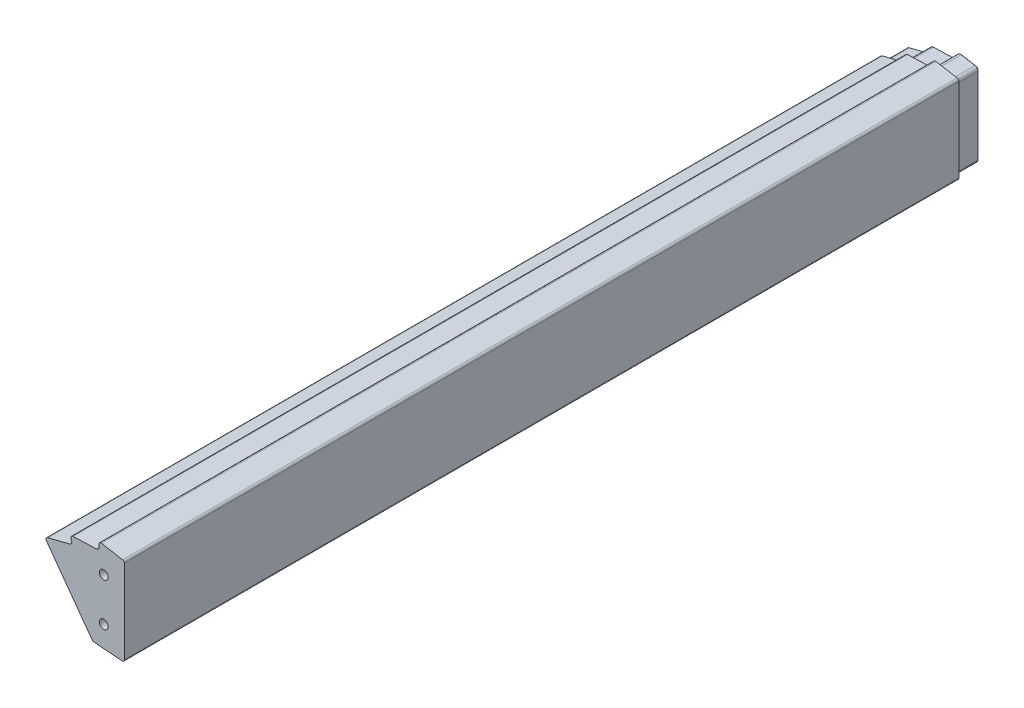
SolidWorks part; units mm, degrees
material "ladder carbon corrected"
ref_plane "Front Plane" through (0, 0, 0) normal (0, 0, 1) x (1, 0, 0)
ref_plane "Top Plane" through (0, 0, 0) normal (0, 1, 0) x (1, 0, 0)
ref_plane "Right Plane" through (0, 0, 0) normal (1, 0, 0) x (0, 0, -1)
sketch "Sketch1" plane through (0, 0, 0) normal (0, 0, 1) x (1, 0, 0)
  line L0 (-19.1269, 28.9196) -> (-2.6193, 27.602)
  line L1 (-46.8997, 66.2532) -> (-20.221, 29.5332)
  line L2 (-46.0481, 68.5905) -> (-33.2024, 71.7845)
  line L3 (-31.1768, 76.652) -> (-17.552, 77.119)
  line L4 (-1, 77.8014) -> (-1, 29.0973)
  line L5 (-14.5587, 81.459) -> (-2.2386, 79.2785)
  line L6 (0, 0) -> (-21.3966, 104.6618) construction
  line L7 (0, 0) -> (-41.6883, 95.6295) construction
  line L8 (-19.7813, 28.3232) -> (5.0398, 26.3421) construction
  line L9 (0, 0) -> (2.1211, 26.575) construction
  line L10 (-30.1863, 29.8023) -> (12.2556, 26.4148) construction
  line L11 (-19.7813, 28.3232) -> (-19.7378, 28.868) construction
  line L12 (-46.4094, 27.8735) -> (21.976, 24.7628) construction
  line L13 (0, 0) -> (0, 116.6603) construction
  line L15 (0, 0) -> (-56.299, 77.489) construction
  line L19 (-16.2897, 79.6815) -> (-16.1338, 78.9186)
  line L20 (-32.5005, 74.5535) -> (-32.1893, 73.8396)
  arc A0 (-33.2024, 71.7845) -> (-32.1893, 73.8396) centre (-33.5643, 73.2402) ccw
  arc A1 (-31.1768, 76.652) -> (-32.5005, 74.5535) centre (-31.1255, 75.1529) ccw
  arc A2 (-17.552, 77.119) -> (-16.1338, 78.9186) centre (-17.6034, 78.6181) ccw
  arc A3 (-14.5587, 81.459) -> (-16.2897, 79.6815) centre (-14.8201, 79.982) ccw
  arc A4 (-2.2386, 79.2785) -> (-1, 77.8014) centre (-2.5, 77.8014) cw
  arc A5 (-46.0481, 68.5905) -> (-46.8997, 66.2532) centre (-45.6861, 67.1348) ccw
  arc A6 (-19.1269, 28.9196) -> (-20.221, 29.5332) centre (-19.0075, 30.4148) cw
  arc A7 (-1, 29.0973) -> (-2.6193, 27.602) centre (-2.5, 29.0973) cw
  circle A8 centre (0, 0) radius 77.675 construction
  dimension "D1" = 1.5
  dimension "D2" = 1.5
  dimension "D11" = 155.35
  dimension "D3" = 2.928
  dimension "D4" = 26.6595
  dimension "D5" = 27.3061
  dimension "D6" = 24.9
  dimension "D7" = 0.5466
  dimension "D8" = 36
  dimension "D9" = 85.437
  dimension "D10" = 1
  dimension "D12" = 11.554
  dimension "D13" = 12
  dimension "D14" = 79.963
  dimension "D15" = 12
  dimension "D16" = 12
extrude "Extrude-Thin1" add sketch "Sketch1" along normal blind 137.5002 and the other way blind 213.5 thin thin type one direction reverse wall 0.27
sketch "Sketch2" plane through (0, 0, 0) normal (0, 0, 1) x (1, 0, 0)
  line L0 (-46.6812, 66.4119) -> (-20.0026, 29.6919) construction
  line L1 (-19.1054, 29.1887) -> (-2.5979, 27.8712) construction
  line L2 (-1.27, 29.0973) -> (-1.27, 77.8014) construction
  line L3 (-46.6812, 66.4119) -> (-20.0026, 29.6919)
  line L4 (-19.1054, 29.1887) -> (-2.5979, 27.8712)
  line L5 (-1.27, 29.0973) -> (-1.27, 77.8014)
  line L6 (-46.6812, 66.4119) -> (-46.7308, 66.48)
  line L31 (-1.27, 77.9505) -> (-1.27, 77.8014)
  line L36 (-2.2638, 79.1357) -> (-14.584, 81.3162)
  line L37 (-16.1477, 79.7106) -> (-15.9917, 78.9476)
  line L38 (-17.547, 76.9741) -> (-31.1719, 76.5071)
  line L39 (-32.3676, 74.6114) -> (-32.0564, 73.8976)
  line L40 (-33.1674, 71.6438) -> (-46.0131, 68.4498)
  line L41 (-2.2638, 79.1357) -> (-14.584, 81.3162)
  line L42 (-16.1477, 79.7106) -> (-15.9917, 78.9476)
  line L43 (-17.547, 76.9741) -> (-31.1719, 76.5071)
  line L44 (-32.3676, 74.6114) -> (-32.0564, 73.8976)
  line L45 (-33.1674, 71.6438) -> (-46.0131, 68.4498)
  arc A0 (-20.0026, 29.6919) -> (-19.1054, 29.1887) centre (-19.0075, 30.4148) ccw construction
  arc A1 (-2.5979, 27.8712) -> (-1.27, 29.0973) centre (-2.5, 29.0973) ccw construction
  arc A2 (-20.0026, 29.6919) -> (-19.1054, 29.1887) centre (-19.0075, 30.4148) ccw
  arc A3 (-2.5979, 27.8712) -> (-1.27, 29.0973) centre (-2.5, 29.0973) ccw
  arc A24 (-46.0131, 68.4498) -> (-46.7308, 66.48) centre (-45.7081, 67.2231) ccw
  arc A25 (-2.2638, 79.1357) -> (-1.27, 77.9505) centre (-2.4736, 77.9505) cw
  arc A28 (-14.584, 81.3162) -> (-16.1477, 79.7106) centre (-14.8201, 79.982) ccw
  arc A29 (-17.547, 76.9741) -> (-15.9917, 78.9476) centre (-17.6034, 78.6181) ccw
  arc A30 (-31.1719, 76.5071) -> (-32.3676, 74.6114) centre (-31.1255, 75.1529) ccw
  arc A31 (-33.1674, 71.6438) -> (-32.0564, 73.8976) centre (-33.5643, 73.2402) ccw
  arc A32 (-14.584, 81.3162) -> (-16.1477, 79.7106) centre (-14.8201, 79.982) ccw
  arc A33 (-17.547, 76.9741) -> (-15.9917, 78.9476) centre (-17.6034, 78.6181) ccw
  arc A34 (-31.1719, 76.5071) -> (-32.3676, 74.6114) centre (-31.1255, 75.1529) ccw
  arc A35 (-33.1674, 71.6438) -> (-32.0564, 73.8976) centre (-33.5643, 73.2402) ccw
  dimension "D1" = 0.125
extrude "Boss-Extrude1" add sketch "Sketch2" along normal offset from surface 75 and the other way offset from surface (288.5 mm away) 75 separate body up to face at (-20.8113, 63.8316, 137.5002) offset beyond the face yes other way up to face at (-20.725, 63.7904, -213.5)
delete or keep bodies "Body-Delete1" type delete bodies bodies 101
sketch "Sketch3" plane through (0, 0, 0) normal (1, 0, 0) x (0, 0, -1)
  line L0 (-212.0001, 103.5239) -> (287.9999, 103.5239)
  line L1 (-212.0001, 103.5239) -> (-212.0001, 3.5239)
  line L2 (287.9999, 103.5239) -> (287.9999, 3.5239)
  line L3 (-212.0001, 3.5239) -> (287.9999, 3.5239)
  line L4 (-212.5003, 53.5239) -> (-212.0001, 53.5239) construction
  line L5 (-212.5003, 29.0973) -> (-212.5002, 77.9505) construction
  line L6 (288.5, 53.5239) -> (287.9999, 53.5239) construction
  line L7 (288.5, 77.9505) -> (288.5, 29.0973) construction
  dimension "D1" = 500
  dimension "D2" = 100
extrude "Cut-Extrude1" cut sketch "Sketch3" against normal through all flip side to cut
hole_wizard "1/4-20 Tapped Hole1" positions "3DSketch1" profile "Sketch4" tap size "1/4-20" standard "ANSI Inch"
sketch3d "3DSketch1"
  line L0 (-13.27, 66.0239, -287.9999) -> (-13.27, 41.0239, -287.9999)
  line L1 (-13.27, 41.0239, -287.9999) -> (-13.27, 41.0239, 212.0001)
  line L2 (-13.27, 41.0239, 212.0001) -> (-13.27, 66.0239, 212.0001)
  line L3 (-13.27, 66.0239, 212.0001) -> (-13.27, 66.0239, -287.9999)
  line L6 (-1.27, 29.0973, 212.0001) -> (-1.27, 77.9505, 212.0001) construction
  line L8 (-13.27, 53.5239, -287.9999) -> (-1.27, 53.5239, -287.9999) construction
  line L10 (-1.27, 77.9505, -287.9999) -> (-1.27, 29.0973, -287.9999) construction
  point P0 (-13.27, 66.0239, 212.0001)
  point P2 (-13.27, 41.0239, 212.0001)
  point P4 (-13.27, 66.0239, -287.9999)
  point P6 (-13.27, 41.0239, -287.9999)
  dimension "D1" = 25
  dimension "D2" = 12
sketch "Sketch4" plane through (-13.27, 66.0239, 212.0001) normal (1, 0, 0) x (0, -1, 0)
  line L0 (0, 0) -> (0, 18.0438)
  line L1 (0, 18.0438) -> (2.5527, 16.51)
  line L2 (2.5527, 16.51) -> (2.5527, 0)
  line L5 (2.5527, 0) -> (0, 0)
  line L10 (0, 18.0438) -> (-2.5527, 16.51) construction
  line L11 (0, -6.35) -> (0, 107.95) construction
  dimension "Tap Drill Dia." = 5.1054
  dimension "Tap Drill Depth" = 16.51
  dimension "Drill Angle" = 118
cosmetic thread "Hole Thread1" parameters "D1"=12.7, "D2"=6.35
cosmetic thread "Hole Thread2" parameters "D1"=12.7, "D2"=6.35
cosmetic thread "Hole Thread3" parameters "D1"=12.7, "D2"=6.35
cosmetic thread "Hole Thread4" parameters "D1"=12.7, "D2"=6.35
sketch "Sketch5" plane through (0, 0, -287.9999) normal (0, 0, -1) x (-1, 0, 0)
  line L113 (2.57, 29.1731) -> (18.9698, 30.4821)
  line L114 (18.9698, 30.4821) -> (45.6477, 67.2011)
  line L115 (45.6477, 67.2011) -> (32.8537, 70.3822)
  line L116 (30.8647, 74.4171) -> (31.1759, 75.1309)
  line L117 (31.1273, 75.2079) -> (17.5025, 75.6749)
  line L118 (14.718, 79.208) -> (14.874, 79.971)
  line L119 (14.8105, 80.0361) -> (2.57, 77.8697)
  line L120 (2.57, 77.8697) -> (2.57, 29.1731)
  line L121 (2.57, 29.1731) -> (18.9698, 30.4821)
  line L122 (18.9698, 30.4821) -> (45.6477, 67.2011)
  line L123 (45.6477, 67.2011) -> (32.8537, 70.3822)
  line L124 (30.8647, 74.4171) -> (31.2082, 75.2051)
  line L125 (31.2082, 75.2051) -> (17.5025, 75.6749)
  line L126 (14.718, 79.208) -> (14.8902, 80.0502)
  line L127 (14.8902, 80.0502) -> (2.57, 77.8697)
  line L128 (2.57, 77.8697) -> (2.57, 29.1731)
  arc A75 (30.8647, 74.4171) -> (32.8537, 70.3822) centre (33.5643, 73.2402) ccw
  arc A76 (31.1759, 75.1309) -> (31.1273, 75.2079) centre (31.1255, 75.1529) ccw
  arc A77 (14.718, 79.208) -> (17.5025, 75.6749) centre (17.6034, 78.6181) ccw
  arc A78 (14.874, 79.971) -> (14.8105, 80.0361) centre (14.8201, 79.982) ccw
  arc A83 (30.8647, 74.4171) -> (32.8537, 70.3822) centre (33.5643, 73.2402) ccw
  arc A85 (14.718, 79.208) -> (17.5025, 75.6749) centre (17.6034, 78.6181) ccw
  dimension "D1" = 1.3
extrude "Cut-Extrude2" cut sketch "Sketch5" against normal blind 13 flip side to cut
fillet "Fillet3" radius 2.1 1 edges at (-31.2082, 75.2051, -281.4999)
fillet "Fillet4" radius 2.1 5 edges at (-2.57, 29.1731, -281.4999) (-18.9698, 30.4821, -281.4999) (-2.57, 77.8697, -281.4999) (-45.6477, 67.2011, -281.4999) (-14.8902, 80.0502, -281.4999)
chamfer "Chamfer1" distance 0.5 angle 45 14 edges at (-44.0907, 66.6338, -287.9999) (-37.739, 69.1675, -287.9999) (-31.6773, 47.9723, -287.9999) (-31.2522, 71.4162, -287.9999) (-18.8662, 30.6668, -287.9999) (-30.0232, 74.6619, -287.9999) (-11.4216, 29.8796, -287.9999) (-23.047, 75.4848, -287.9999) (-3.2454, 29.9045, -287.9999) (-15.721, 76.3533, -287.9999) (-2.57, 53.778, -287.9999) (-13.8441, 79.2725, -287.9999) (-3.0609, 77.458, -287.9999) (-8.308, 78.8852, -287.9999)
